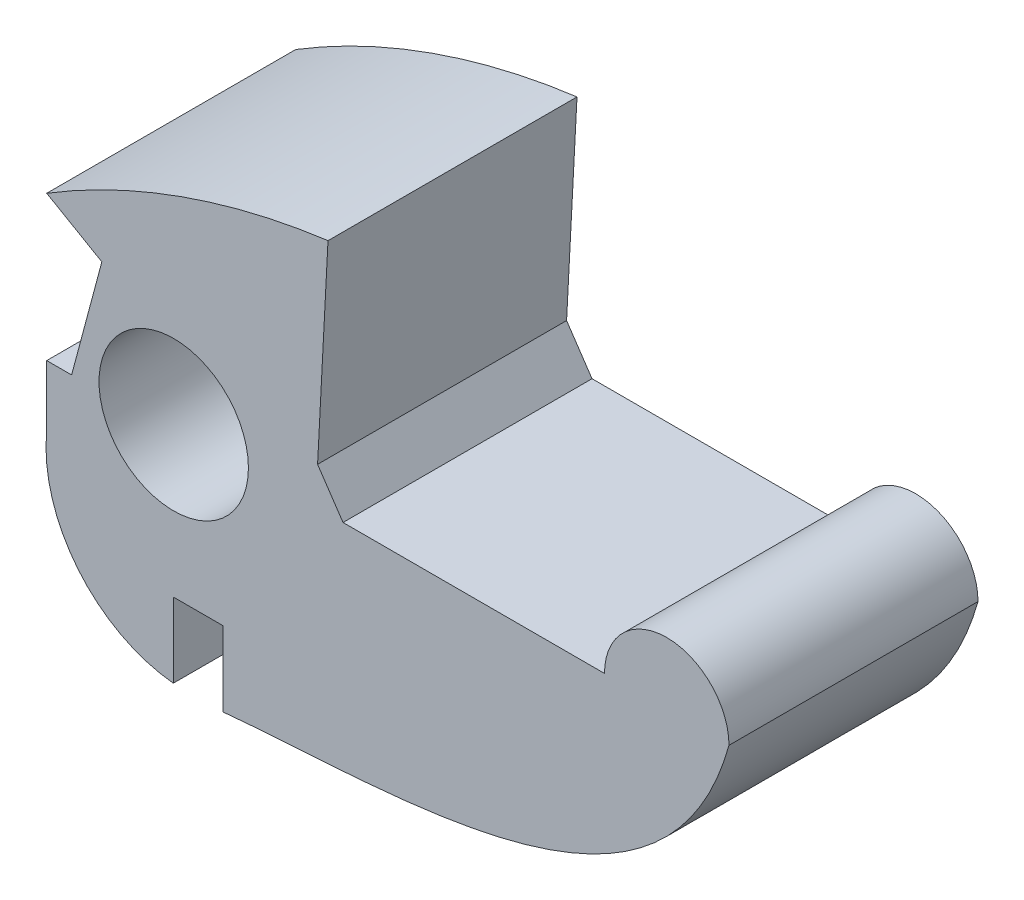
SolidWorks part; units mm, degrees
ref_plane "Front Plane" through (0, 0, 0) normal (0, 0, 1) x (1, 0, 0)
ref_plane "Top Plane" through (0, 0, 0) normal (0, 1, 0) x (1, 0, 0)
ref_plane "Right Plane" through (0, 0, 0) normal (1, 0, 0) x (0, 0, -1)
sketch "Sketch1" plane through (0, 0, 0) normal (0, 0, 1) x (1, 0, 0)
  line L0 (-11.9, -9) -> (-11.9, 9.5) construction
  line L1 (-11.9, 9.5) -> (-0.6036, 9.5) construction
  line L2 (0, 0) -> (0.4979, 9.5) construction
  line L3 (0, 0) -> (15.5, 0)
  line L4 (15.5, 0) -> (15.5, -9) construction
  line L5 (15.5, -9) -> (-11.9, -9) construction
  line L6 (-0.6036, 9.5) -> (-1.0223, 1.511)
  line L7 (-1.0223, 1.511) -> (0, 0)
  line L8 (0.4979, 9.5) -> (-0.6036, 9.5) construction
  line L9 (0, 0) -> (-6.8, 0) construction
  line L10 (-11.9, -9) -> (-6.2431, -3.3431) construction
  line L11 (-6.817, -9) -> (-6.817, -6)
  line L12 (-11.9, 5.5) -> (-9.686, 4.2218)
  line L13 (-6.817, -6) -> (-4.817, -6)
  line L14 (-4.817, -6) -> (-4.817, -9)
  line L15 (-4.817, -9) -> (15.5, -9) construction
  line L16 (-6.8, 0) -> (-6.8, 6) construction
  line L17 (-9.686, 4.2218) -> (-10.9, -0.3188)
  line L18 (-10.9, -0.3188) -> (-11.9, -0.3188)
  line L19 (-11.9, -0.3188) -> (-11.9, -2.7693)
  line L20 (-11.9, 5.5) -> (-11.9, 9.5) construction
  line L21 (-6.8, 0) -> (-0.6036, 9.5) construction
  line L22 (-0.6036, 9.5) -> (-0.6036, 0) construction
  circle A0 centre (13, 0) radius 2.5
  circle A1 centre (-6.8, 0) radius 3
  arc A2 (-11.9, -2.7693) -> (-6.817, -9) centre (-6.2431, -3.3431) ccw
  arc A3 (-11.9, 5.5) -> (-0.6036, 9.5) centre (3.1197, -18.9661) cw
  spline S0 degree 3 poles (15.5, 0) (12.976, -9.011) (2.1152, -8.3313) (-4.817, -9) knots 0 0 0 0 1 1 1 1
  dimension "D6" = 2.5
  dimension "D9" = 6
  dimension "D13" = 5.6859
  dimension "D23" = 28.7085
  dimension "D1" = 87
  dimension "D2" = 9
  dimension "D3" = 27.4
  dimension "D4" = 18.5
  dimension "D5" = 15.5
  dimension "D7" = 1.1
  dimension "D8" = 8
  dimension "D10" = 6.8
  dimension "D11" = 8
  dimension "D12" = 45
  dimension "D14" = 2
  dimension "D15" = 3
  dimension "D16" = 6
  dimension "D17" = 2.5565
  dimension "D18" = 4.7
  dimension "D19" = 120
  dimension "D20" = 4
  dimension "D21" = 1
extrude "Boss-Extrude1" add sketch "Sketch1" along normal blind 10
